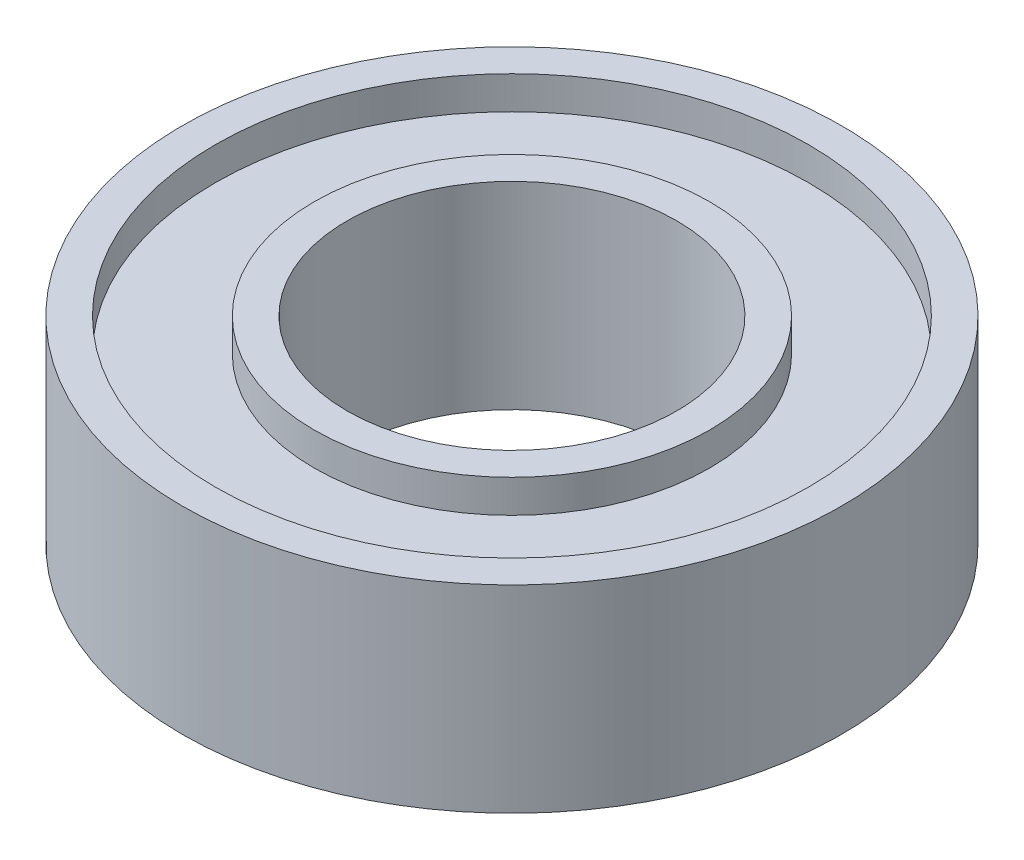
SolidWorks part; units mm, degrees
ref_plane "Alzado" through (0, 0, 0) normal (0, 0, 1) x (1, 0, 0)
ref_plane "Planta" through (0, 0, 0) normal (0, 1, 0) x (1, 0, 0)
ref_plane "Vista lateral" through (0, 0, 0) normal (1, 0, 0) x (0, 0, -1)
sketch "Croquis2" plane through (0, 0, 0) normal (0, 1, 0) x (1, 0, 0)
  circle A0 centre (0, 0) radius 5
  circle A1 centre (0, 0) radius 2.5
  dimension "D1" = 5
  dimension "D2" = 10
extrude "Saliente-Extruir1" add sketch "Croquis2" along normal blind 3
sketch "Croquis3" plane through (0, 3, 0) normal (0, 1, 0) x (1, 0, 0)
  circle A0 centre (0, 0) radius 3
  circle A1 centre (0, 0) radius 4.5
  circle A2 centre (0, 0) radius 5 construction
  circle A3 centre (0, 0) radius 2.5 construction
  dimension "D1" = 0.5
  dimension "D2" = 0.5
extrude "Cortar-Extruir1" cut sketch "Croquis3" against normal blind 0.5
ref_plane "Plano1" through (0, 1.5, 0) normal (0, 1, 0) x (1, 0, 0)
mirror "Simetría1" about plane through (0, 1.5, 0) normal (0, 1, 0) of "Cortar-Extruir1"
